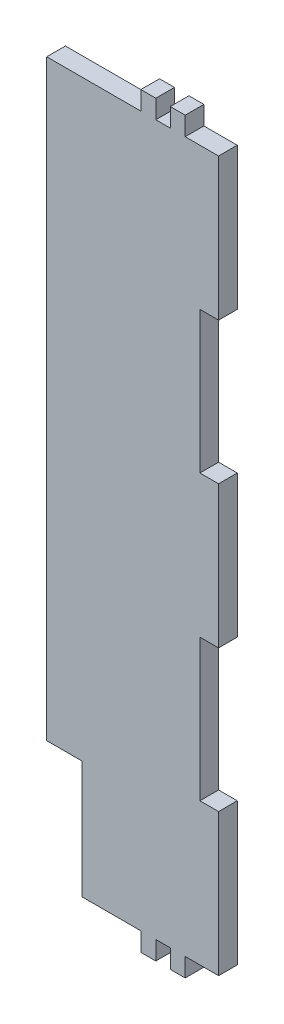
SolidWorks part; units mm, degrees
ref_plane "Front Plane" through (0, 0, 0) normal (0, 0, 1) x (1, 0, 0)
ref_plane "Top Plane" through (0, 0, 0) normal (0, 1, 0) x (1, 0, 0)
ref_plane "Right Plane" through (0, 0, 0) normal (1, 0, 0) x (0, 0, -1)
sketch "Sketch1" plane through (0, 0, 0) normal (0, 0, 1) x (1, 0, 0)
  line L0 (-12.5, 0) -> (12.5, 0) construction
  line L1 (12.5, 120.6625) -> (-12.5, 120.6625)
  line L2 (12.5, 120.6625) -> (12.5, -120.6625)
  line L3 (12.5, -120.6625) -> (-12.5, -120.6625)
  line L4 (-12.5, 120.6625) -> (-12.5, -120.6625)
  line L5 (12.5, 120.6625) -> (-12.5, -120.6625) construction
  line L6 (12.5, -120.6625) -> (-12.5, 120.6625) construction
  line L7 (12.5, 72.3975) -> (18.85, 72.3975)
  line L8 (12.5, 72.3975) -> (12.5, 24.1325)
  line L9 (12.5, 24.1325) -> (18.85, 24.1325)
  line L11 (12.5, -24.1325) -> (18.85, -24.1325)
  line L12 (12.5, -24.1325) -> (12.5, -72.3975)
  line L13 (12.5, -72.3975) -> (18.85, -72.3975)
  line L15 (7.5, -120.6625) -> (7.5, -127.0125)
  line L16 (-7.5, 120.6625) -> (-2.5, 120.6625)
  line L17 (-7.5, 120.6625) -> (-7.5, 127.0125)
  line L18 (-7.5, 127.0125) -> (-2.5, 127.0125)
  line L19 (-2.5, 120.6625) -> (-2.5, 127.0125)
  line L20 (2.5, 120.6625) -> (7.5, 120.6625)
  line L21 (2.5, 120.6625) -> (2.5, 127.0125)
  line L22 (2.5, 127.0125) -> (7.5, 127.0125)
  line L23 (7.5, 120.6625) -> (7.5, 127.0125)
  line L24 (2.5, -127.0125) -> (7.5, -127.0125)
  line L25 (2.5, -120.6625) -> (2.5, -127.0125)
  line L26 (-2.5, -120.6625) -> (-2.5, -127.0125)
  line L27 (-7.5, -127.0125) -> (-2.5, -127.0125)
  line L28 (-7.5, -120.6625) -> (-7.5, -127.0125)
  line L29 (12.5, 120.6625) -> (18.85, 120.6625)
  line L30 (18.85, 120.6625) -> (18.85, 72.3975)
  line L31 (18.85, 24.1325) -> (18.85, -24.1325)
  line L32 (12.5, -120.6625) -> (18.85, -120.6625)
  line L33 (18.85, -120.6625) -> (18.85, -72.3975)
  line L35 (-12.5, 120.6625) -> (-27.5, 120.6625)
  line L36 (-12.5, 120.6625) -> (-12.5, -120.6625)
  line L37 (-12.5, -120.6625) -> (-27.5, -120.6625)
  line L38 (-27.5, 120.6625) -> (-27.5, -120.6625)
  line L39 (-27.5, 120.6625) -> (-39.5, 120.6625)
  line L40 (-27.5, 120.6625) -> (-27.5, -80.6625)
  line L41 (-27.5, -80.6625) -> (-39.5, -80.6625)
  line L42 (-39.5, 120.6625) -> (-39.5, -80.6625)
  point P0 (0, 0)
  dimension "D1" = 241.325
  dimension "D2" = 25
  dimension "D3" = 6.35
  dimension "D4" = 48.265
  dimension "D5" = 48.265
  dimension "D6" = 6.35
  dimension "D7" = 48.265
  dimension "D8" = 48.265
  dimension "D9" = 5
  dimension "D10" = 5
  dimension "D11" = 5
  dimension "D12" = 5
  dimension "D13" = 6.35
  dimension "D14" = 6.35
  dimension "D15" = 6.35
  dimension "D16" = 6.35
  dimension "D17" = 15
  dimension "D18" = 12
  dimension "D19" = 40
extrude "Boss-Extrude1" add sketch "Sketch1" along normal blind 6.35
sketch "Sketch3" plane through (0, 0, 6.35) normal (0, 0, 1) x (1, 0, 0)
  line L28 (-27.5406, -80.7031) -> (-27.5406, -120.7031)
  line L29 (-27.5406, -80.7031) -> (-27.5406, -120.7031)
  line L32 (-39.5406, 120.7031) -> (-39.5406, -80.7031)
  line L33 (-39.5406, 120.7031) -> (-39.5406, -80.7031)
  line L34 (-39.5406, -80.7031) -> (-27.5406, -80.7031)
  line L35 (-39.5406, -80.7031) -> (-27.5406, -80.7031)
  line L56 (18.8906, 120.7031) -> (7.5406, 120.7031)
  line L57 (7.5406, 120.7031) -> (7.5406, 127.0531)
  line L58 (7.5406, 127.0531) -> (2.4594, 127.0531)
  line L59 (2.4594, 127.0531) -> (2.4594, 120.7031)
  line L60 (2.4594, 120.7031) -> (-2.4594, 120.7031)
  line L61 (-2.4594, 120.7031) -> (-2.4594, 127.0531)
  line L62 (-2.4594, 127.0531) -> (-7.5406, 127.0531)
  line L63 (-7.5406, 127.0531) -> (-7.5406, 120.7031)
  line L64 (-7.5406, 120.7031) -> (-39.5406, 120.7031)
  line L66 (-27.5406, -120.7031) -> (-7.5406, -120.7031)
  line L67 (-7.5406, -120.7031) -> (-7.5406, -127.0531)
  line L68 (-7.5406, -127.0531) -> (-2.4594, -127.0531)
  line L69 (-2.4594, -127.0531) -> (-2.4594, -120.7031)
  line L70 (-2.4594, -120.7031) -> (2.4594, -120.7031)
  line L71 (2.4594, -120.7031) -> (2.4594, -127.0531)
  line L72 (2.4594, -127.0531) -> (7.5406, -127.0531)
  line L73 (7.5406, -127.0531) -> (7.5406, -120.7031)
  line L74 (7.5406, -120.7031) -> (18.8906, -120.7031)
  line L75 (18.8906, -120.7031) -> (18.8906, -72.3569)
  line L76 (18.8906, -72.3569) -> (12.5406, -72.3569)
  line L77 (12.5406, -72.3569) -> (12.5406, -24.1731)
  line L78 (12.5406, -24.1731) -> (18.8906, -24.1731)
  line L79 (18.8906, -24.1731) -> (18.8906, 24.1731)
  line L80 (18.8906, 24.1731) -> (12.5406, 24.1731)
  line L81 (12.5406, 24.1731) -> (12.5406, 72.3569)
  line L82 (12.5406, 72.3569) -> (18.8906, 72.3569)
  line L83 (18.8906, 72.3569) -> (18.8906, 120.7031)
  line L84 (18.8906, 120.7031) -> (7.5406, 120.7031)
  line L85 (7.5406, 120.7031) -> (7.5406, 127.0531)
  line L86 (7.5406, 127.0531) -> (2.4594, 127.0531)
  line L87 (2.4594, 127.0531) -> (2.4594, 120.7031)
  line L88 (2.4594, 120.7031) -> (-2.4594, 120.7031)
  line L89 (-2.4594, 120.7031) -> (-2.4594, 127.0531)
  line L90 (-2.4594, 127.0531) -> (-7.5406, 127.0531)
  line L91 (-7.5406, 127.0531) -> (-7.5406, 120.7031)
  line L92 (-7.5406, 120.7031) -> (-39.5406, 120.7031)
  line L94 (-27.5406, -120.7031) -> (-7.5406, -120.7031)
  line L95 (-7.5406, -120.7031) -> (-7.5406, -127.0531)
  line L96 (-7.5406, -127.0531) -> (-2.4594, -127.0531)
  line L97 (-2.4594, -127.0531) -> (-2.4594, -120.7031)
  line L98 (-2.4594, -120.7031) -> (2.4594, -120.7031)
  line L99 (2.4594, -120.7031) -> (2.4594, -127.0531)
  line L100 (2.4594, -127.0531) -> (7.5406, -127.0531)
  line L101 (7.5406, -127.0531) -> (7.5406, -120.7031)
  line L102 (7.5406, -120.7031) -> (18.8906, -120.7031)
  line L103 (18.8906, -120.7031) -> (18.8906, -72.3569)
  line L104 (18.8906, -72.3569) -> (12.5406, -72.3569)
  line L105 (12.5406, -72.3569) -> (12.5406, -24.1731)
  line L106 (12.5406, -24.1731) -> (18.8906, -24.1731)
  line L107 (18.8906, -24.1731) -> (18.8906, 24.1731)
  line L108 (18.8906, 24.1731) -> (12.5406, 24.1731)
  line L109 (12.5406, 24.1731) -> (12.5406, 72.3569)
  line L110 (12.5406, 72.3569) -> (18.8906, 72.3569)
  line L111 (18.8906, 72.3569) -> (18.8906, 120.7031)
  dimension "D1" = 0.0406
extrude "Boss-Extrude2" add sketch "Sketch3" against normal up to surface (6.35 mm away) up to face at (0.97, -5.3775, 0)
